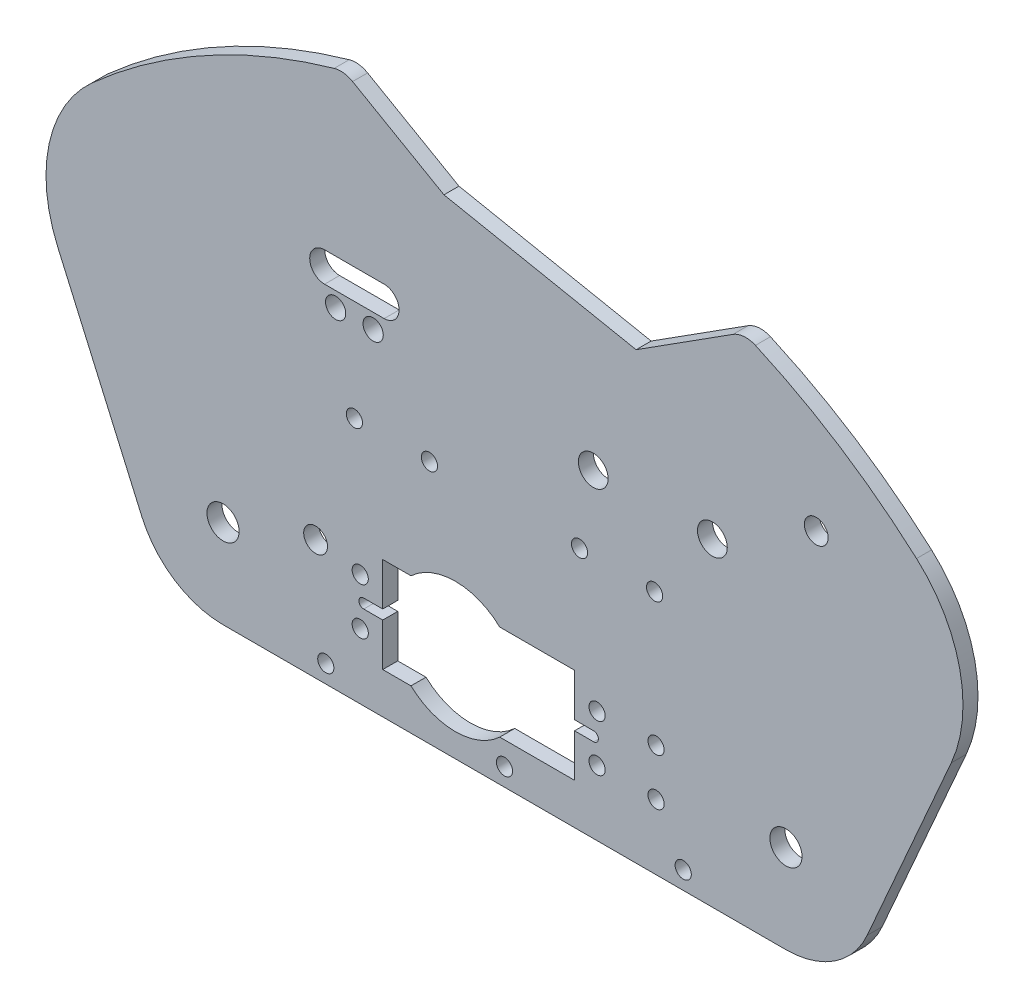
SolidWorks part; units mm, degrees
ref_plane "Front Plane" through (0, 0, 0) normal (0, 0, 1) x (1, 0, 0)
ref_plane "Top Plane" through (0, 0, 0) normal (0, 1, 0) x (1, 0, 0)
ref_plane "Right Plane" through (0, 0, 0) normal (1, 0, 0) x (0, 0, -1)
sketch "Sketch1" plane through (0, 0, 0) normal (0, 0, 1) x (1, 0, 0)
  line L8 (0, 18.9078) -> (120.015, 18.9078) construction
  line L18 (155.2575, 52.1157) -> (-35.2425, 52.1157) construction
  line L37 (0, 0) -> (120.015, 0)
  line L42 (19.7347, 25.5664) -> (0, 18.9078) construction
  line L54 (155.2575, 52.1157) -> (137.3256, 11.3022)
  line L55 (60.0075, 52.1157) -> (60.0075, 18.9078) construction
  line L56 (-35.2425, 52.1157) -> (-17.3106, 11.3022)
  line L58 (147.8628, 86.1549) -> (-27.8478, 86.1549) construction
  circle A21 centre (120.015, 18.9078) radius 3.429
  circle A22 centre (0, 18.9078) radius 3.429
  arc A25 (137.3256, 11.3022) -> (120.015, 0) centre (120.015, 18.9078) cw
  arc A26 (0, 0) -> (-17.3106, 11.3022) centre (0, 18.9078) cw
  circle A27 centre (19.7347, 25.5664) radius 2.54
  arc A28 (147.8628, 86.1549) -> (-27.8478, 86.1549) centre (60.0075, -12.2157) ccw
  arc A29 (147.8628, 86.1549) -> (155.2575, 52.1157) centre (128.1135, 64.0417) cw
  arc A30 (-27.8478, 86.1549) -> (-35.2425, 52.1157) centre (-8.0985, 64.0417) ccw
  dimension "D5" = 18.9078
  dimension "D8" = 29.6484
  dimension "D3" = 52.1157
  dimension "D2" = 6.858
  dimension "D10" = 5.08
  dimension "D1" = 190.5
  dimension "D4" = 20.8278
  dimension "D6" = 18.645
  dimension "D7" = 120.015
  dimension "D9" = 34.0392
extrude "Boss-Extrude1" add sketch "Sketch1" along normal blind 3.2004
sketch "Sketch2" plane through (0, 0, 0) normal (0, 0, -1) x (-1, 0, 0)
  line L1 (-155.2575, 52.1157) -> (35.2425, 52.1157) construction
  line L28 (-92.0115, 52.1157) -> (-76.0095, 52.1157) construction
  line L29 (-76.0095, 52.1157) -> (-44.0055, 52.1157) construction
  line L30 (-44.0055, 52.1157) -> (-28.0035, 52.1157) construction
  circle A0 centre (-92.0115, 52.1157) radius 1.7272
  circle A1 centre (-76.0095, 52.1157) radius 1.7272
  circle A2 centre (-44.0055, 52.1157) radius 1.7272
  circle A3 centre (-28.0035, 52.1157) radius 1.7272
  point P11 (-36.0045, 52.1157)
  point P16 (-84.0105, 52.1157)
  dimension "D3" = 3.4544
  dimension "D2" = 16.002
  dimension "D4" = 48.006
extrude "Cut-Extrude1" cut sketch "Sketch2" against normal blind 3.2004
sketch "Sketch5" plane through (0, 0, 0) normal (0, 0, -1) x (-1, 0, 0)
  line L0 (0, 18.9078) -> (-120.015, 18.9078) construction
  line L5 (-92.3222, 13.9078) -> (-92.3222, 23.9078) construction
  line L6 (-74.944, 29.0678) -> (-74.944, 8.7478)
  line L7 (-34.05, 29.0678) -> (-34.05, 8.7478)
  line L12 (-54.497, 29.0678) -> (-54.497, 8.7478) construction
  line L13 (-79.747, 13.9078) -> (-79.747, 23.9078) construction
  line L14 (-29.247, 13.9078) -> (-29.247, 23.9078) construction
  line L15 (-79.747, 18.9078) -> (-29.247, 18.9078) construction
  line L19 (-92.3222, 18.9078) -> (-79.747, 18.9078) construction
  line L21 (-74.944, 8.7478) -> (-34.05, 8.7478)
  line L25 (-74.944, 29.0678) -> (-34.05, 29.0678)
  circle A0 centre (-79.747, 23.9078) radius 1.7272
  circle A1 centre (-29.247, 13.9078) radius 1.7272
  circle A2 centre (-29.247, 23.9078) radius 1.7272
  circle A3 centre (-79.747, 13.9078) radius 1.7272
  circle A6 centre (0, 18.9078) radius 3.429 construction
  circle A9 centre (-92.3222, 23.9078) radius 1.7272
  circle A10 centre (-92.3222, 13.9078) radius 1.7272
  point P8 (-44.45, 18.9078)
  point P9 (-54.497, 18.9078)
  dimension "D2" = 3.4544
  dimension "D3" = 40.894
  dimension "D5" = 10.4
  dimension "D1" = 50.5
  dimension "D4" = 20.32
  dimension "D6" = 44.45
  dimension "D7" = 10
  dimension "D8" = 12.5752
extrude "Cut-Extrude3" cut sketch "Sketch5" against normal through all
sketch "Sketch6" plane through (0, 0, 3.2004) normal (0, 0, 1) x (1, 0, 0)
  line L3 (79.747, 18.9078) -> (29.247, 18.9078) construction
  line L4 (29.986, 19.9238) -> (34.05, 19.9238)
  line L5 (29.986, 19.9238) -> (29.986, 17.8918) construction
  line L7 (29.986, 17.8918) -> (34.05, 17.8918)
  line L8 (34.05, 19.9238) -> (34.05, 17.8918)
  line L9 (74.944, 19.9238) -> (79.008, 19.9238)
  line L10 (74.944, 19.9238) -> (74.944, 17.8918)
  line L11 (74.944, 17.8918) -> (79.008, 17.8918)
  line L12 (79.008, 19.9238) -> (79.008, 17.8918) construction
  line L13 (34.05, 8.7478) -> (34.05, 29.0678) construction
  line L14 (74.944, 29.0678) -> (74.944, 8.7478) construction
  arc A6 (79.008, 19.9238) -> (79.008, 17.8918) centre (79.008, 18.9078) cw
  arc A7 (29.986, 19.9238) -> (29.986, 17.8918) centre (29.986, 18.9078) ccw
  point P22 (34.05, 18.9078)
  point P23 (74.944, 18.9078)
  dimension "D4" = 4.064
  dimension "D5" = 2.032
extrude "Cut-Extrude4" cut sketch "Sketch6" against normal up to surface (3.2004 mm away) up to face at (90.595, 23.9078, 0)
sketch "Sketch8" plane through (0, 0, 3.2004) normal (0, 0, 1) x (1, 0, 0)
  line L0 (21.9075, 3.81) -> (98.1075, 3.81) construction
  line L1 (60.0075, 7.62) -> (60.0075, 0) construction
  line L2 (0, 0) -> (120.015, 0) construction
  circle A0 centre (21.9075, 3.81) radius 1.7272
  circle A1 centre (60.0075, 3.81) radius 1.7272
  circle A2 centre (98.1075, 3.81) radius 1.7272
  point P6 (60.0075, 3.81)
  dimension "D3" = 3.4544
  dimension "D1" = 76.2
  dimension "D2" = 7.62
extrude "Cut-Extrude6" cut sketch "Sketch8" against normal up to surface (3.2004 mm away) up to face at (54.497, 18.9078, 0)
sketch "Sketch9" plane through (0, 0, 3.2004) normal (0, 0, 1) x (1, 0, 0)
  line L0 (146.2916, 31.7089) -> (111.6995, 46.9073) construction
  line L1 (111.6995, 46.9073) -> (126.4745, 80.5358) construction
  line L3 (137.3256, 11.3022) -> (155.2575, 52.1157) construction
  circle A0 centre (126.4745, 80.5358) radius 2.54
  circle A2 centre (19.7347, 25.5664) radius 2.54 construction
  dimension "D1" = 37.7837
  dimension "D2" = 36.7311
extrude "Cut-Extrude7" cut sketch "Sketch9" against normal up to surface (3.2004 mm away) up to face at (20.1803, 3.81, 0)
sketch "Sketch10" plane through (0, 0, 3.2004) normal (0, 0, 1) x (1, 0, 0)
  line L0 (25.7818, 115.1575) -> (47.0979, 102.9327)
  line L1 (47.0979, 102.9327) -> (88.0719, 94.8169)
  line L2 (88.0719, 94.8169) -> (110.9924, 109.4226)
  arc A1 (147.8628, 86.1549) -> (-27.8478, 86.1549) centre (60.0075, -12.2157) ccw construction
  arc A2 (110.9924, 109.4226) -> (25.7818, 115.1575) centre (60.0075, -12.2157) ccw
  point P0 (43.3022, 118.6134)
  dimension "D1" = 41.77
  dimension "D2" = 27.1786
  dimension "D3" = 17.858
  dimension "D4" = 24.5728
  dimension "D5" = 161.37
  dimension "D6" = 136.29
extrude "Cut-Extrude8" cut sketch "Sketch10" against normal up to surface (3.2004 mm away) up to face at (123.9345, 80.5358, 0)
fillet "Fillet1" radius 5.08 2 edges at (25.7818, 115.1575, 1.6002) (110.9924, 109.4226, 1.6002)
sketch "Sketch12" plane through (0, 0, 3.2004) normal (0, 0, 1) x (1, 0, 0)
  line L1 (21.6535, 80.0557) -> (34.3535, 80.0557)
  line L2 (21.6535, 80.0557) -> (21.6535, 73.7057) construction
  line L3 (21.6535, 73.7057) -> (34.3535, 73.7057)
  line L4 (34.3535, 80.0557) -> (34.3535, 73.7057) construction
  line L7 (0, 0) -> (120.015, 0) construction
  line L9 (28.0035, 73.7057) -> (28.0035, 70.5307) construction
  line L11 (24.003, 70.5307) -> (32.004, 70.5307) construction
  arc A0 (34.3535, 80.0557) -> (34.3535, 73.7057) centre (34.3535, 76.8807) cw
  arc A1 (21.6535, 80.0557) -> (21.6535, 73.7057) centre (21.6535, 76.8807) ccw
  circle A6 centre (28.0035, 52.1157) radius 1.7272 construction
  circle A7 centre (24.003, 70.5307) radius 2.159
  circle A8 centre (32.004, 70.5307) radius 2.159
  dimension "D3" = 6.35
  dimension "D4" = 21.59
  dimension "D5" = 4.318
  dimension "D1" = 12.7
  dimension "D2" = 6.35
  dimension "D6" = 3.175
  dimension "D7" = 8.001
extrude "Cut-Extrude10" cut sketch "Sketch12" against normal up to surface (3.2004 mm away) up to face at (63.4319, 67.4563, 0)
sketch "Sketch13" plane through (0, 0, 3.2004) normal (0, 0, 1) x (1, 0, 0)
  line L0 (79.747, 18.9078) -> (29.247, 18.9078) construction
  circle A0 centre (49.53, 18.9078) radius 13.8852
  dimension "D1" = 27.7704
  dimension "D2" = 5.08
extrude "Cut-Extrude11" cut sketch "Sketch13" against normal up to surface (3.2004 mm away) up to face at (28.0035, 76.8807, 0)
sketch "Sketch14" plane through (0, 0, 3.2004) normal (0, 0, 1) x (1, 0, 0)
  line L0 (78.9305, 67.9907) -> (104.3305, 67.9907) construction
  line L1 (84.0105, 67.9907) -> (84.0105, 52.1157) construction
  line L2 (92.0115, 52.1157) -> (76.0095, 52.1157) construction
  circle A0 centre (78.9305, 67.9907) radius 3.175
  circle A1 centre (104.3305, 67.9907) radius 3.175
  point P0 (91.6305, 67.9907)
  dimension "D1" = 6.35
  dimension "D2" = 25.4
  dimension "D3" = 15.875
  dimension "D4" = 7.62
extrude "Cut-Extrude12" cut sketch "Sketch14" against normal up to surface (3.2004 mm away) up to face at (53.2552, 18.9078, 0)
